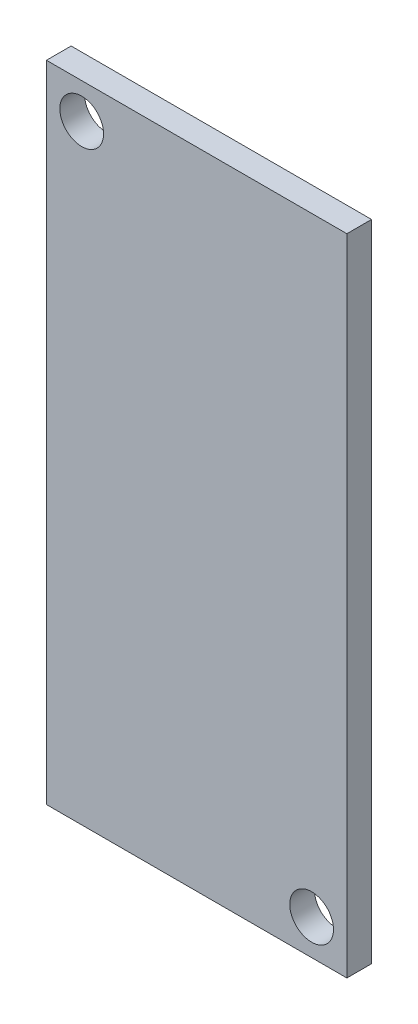
SolidWorks part; units mm, degrees
ref_plane "Front Plane" through (0, 0, 0) normal (0, 0, 1) x (1, 0, 0)
ref_plane "Top Plane" through (0, 0, 0) normal (0, 1, 0) x (1, 0, 0)
ref_plane "Right Plane" through (0, 0, 0) normal (1, 0, 0) x (0, 0, -1)
sketch "Sketch1" plane through (0, 0, 0) normal (0, 0, 1) x (1, 0, 0)
  line L0 (10.65, 0) -> (-10.65, 0) construction
  line L1 (-10.65, 22.85) -> (10.65, 22.85)
  line L2 (-10.65, 22.85) -> (-10.65, -22.85)
  line L3 (-10.65, -22.85) -> (10.65, -22.85)
  line L4 (10.65, 22.85) -> (10.65, -22.85)
  dimension "D1" = 21.3
  dimension "D2" = 45.7
extrude "Extrude1" add sketch "Sketch1" along normal blind 1.75
sketch "Sketch2" plane through (0, 0, 1.75) normal (0, 0, 1) x (1, 0, 0)
  line L0 (-10.65, -22.85) -> (10.65, -22.85) construction
  line L1 (-10.65, 22.85) -> (-10.65, -22.85) construction
  line L2 (10.65, 22.85) -> (-10.65, 22.85) construction
  line L3 (10.65, -22.85) -> (10.65, 22.85) construction
  circle A0 centre (8.15, -20.35) radius 1.55
  circle A1 centre (-8.15, 20.35) radius 1.55
  dimension "D1" = 3.1
  dimension "D2" = 2.5
  dimension "D3" = 2.5
  dimension "D4" = 3.1
  dimension "D5" = 2.5
  dimension "D6" = 2.5
extrude "Cut-Extrude1" cut sketch "Sketch2" against normal up to surface (1.75 mm away) up to face at (0, 0, 0)
